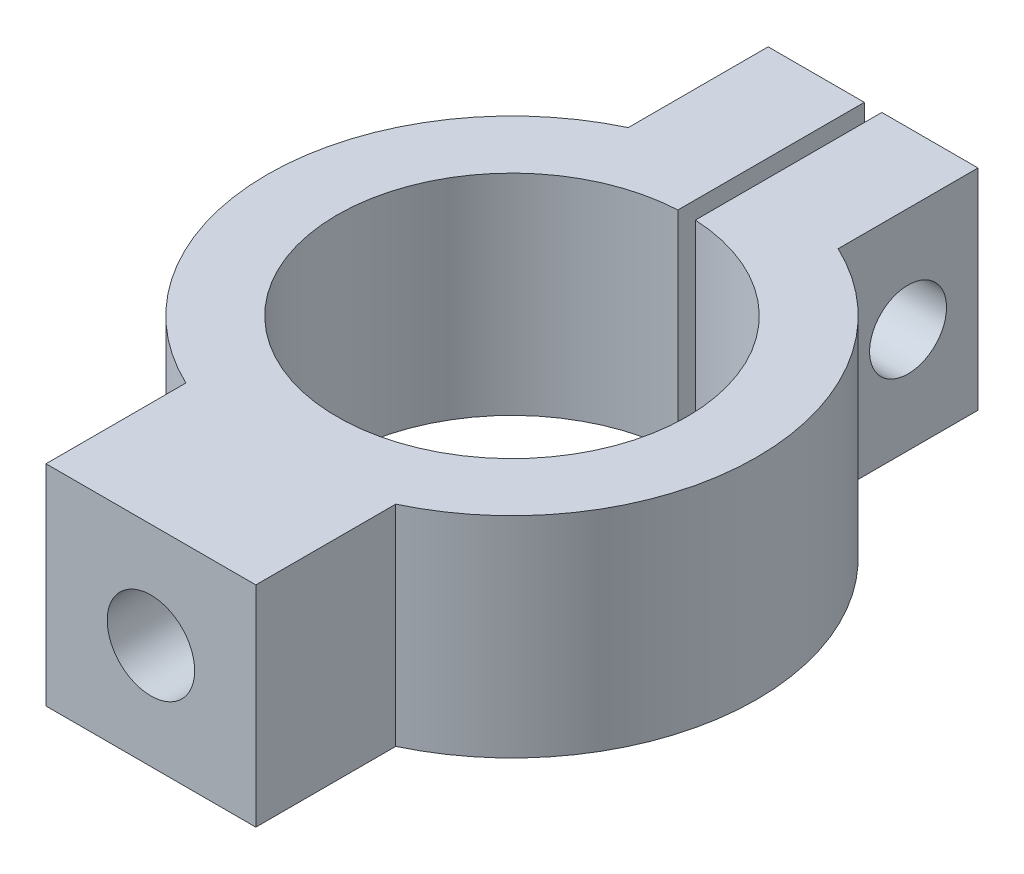
SolidWorks part; units mm, degrees
ref_plane "Front Plane" through (0, 0, 0) normal (0, 0, 1) x (1, 0, 0)
ref_plane "Top Plane" through (0, 0, 0) normal (0, 1, 0) x (1, 0, 0)
ref_plane "Right Plane" through (0, 0, 0) normal (1, 0, 0) x (0, 0, -1)
sketch "Loop Sketch" plane through (0, 0, 0) normal (0, 1, 0) x (1, 0, 0)
  circle A0 centre (0, 0) radius 7
  circle A1 centre (0, 0) radius 5
  dimension "D1" = 14
  dimension "D2" = 10
extrude "Loop Extrude" add sketch "Loop Sketch" along normal blind 6
sketch "Block Sketch" plane through (0, 0, 0) normal (0, 1, 0) x (1, 0, 0)
  line L1 (-3, -10.3246) -> (3, -10.3246)
  line L2 (-3, -10.3246) -> (-3, -6.3246)
  line L3 (-3, -6.3246) -> (3, -6.3246)
  line L4 (3, -10.3246) -> (3, -6.3246)
  line L5 (-3, -10.3246) -> (3, -6.3246) construction
  line L6 (-3, -6.3246) -> (3, -10.3246) construction
  line L7 (3, 10.3246) -> (-3, 10.3246)
  line L8 (3, 10.3246) -> (3, 6.3246)
  line L9 (3, 6.3246) -> (-3, 6.3246)
  line L10 (-3, 10.3246) -> (-3, 6.3246)
  line L11 (3, 10.3246) -> (-3, 6.3246) construction
  line L12 (3, 6.3246) -> (-3, 10.3246) construction
  circle A0 centre (0, 0) radius 7 construction
  circle A2 centre (0, 0) radius 7 construction
  point P0 (0, -8.3246)
  point P7 (0, 8.3246)
  dimension "D1" = 6
  dimension "D2" = 4
extrude "Block Extrude" add sketch "Block Sketch" along normal up to surface (6 mm away) up to face at (0, 6, 7)
sketch "Slot Sketch" plane through (0, 0, 0) normal (0, 1, 0) x (1, 0, 0)
  line L5 (3, 10.3246) -> (-3, 10.3246) construction
  line L6 (-0.25, 4.9937) -> (0.25, 4.9937)
  line L7 (-0.25, 4.9937) -> (-0.25, 10.3246)
  line L8 (-0.25, 10.3246) -> (0.25, 10.3246)
  line L9 (0.25, 4.9937) -> (0.25, 10.3246)
  line L10 (-0.25, 4.9937) -> (0.25, 10.3246) construction
  line L11 (-0.25, 10.3246) -> (0.25, 4.9937) construction
  circle A0 centre (0, 0) radius 5 construction
  point P0 (0, 7.6592)
  dimension "D1" = 0.5
extrude "Slot Cut" cut sketch "Slot Sketch" along normal up to surface (6 mm away) up to face at (0, 6, 0)
sketch "M3 Hole Location" plane through (0, 0, 0) normal (0, 0, 1) x (1, 0, 0)
  line L0 (-3, 6) -> (-3, 0) construction
  point P0 (0, 3)
  point P4 (-3, 3)
hole_wizard "M3x0.5 Tapped Hole1" positions "Sketch5" profile "Sketch6" tap size "M3x0.5" standard "ANSI Metric"
sketch "Sketch5" plane through (0, 0, 10.3246) normal (0, 0, 1) x (1, 0, 0)
  point P0 (0, 3)
sketch "Sketch6" plane through (0, 3, 10.3246) normal (1, 0, 0) x (0, -1, 0)
  line L0 (0, 0) -> (0, 4.7511)
  line L1 (0, 4.7511) -> (1.25, 4)
  line L2 (1.25, 4) -> (1.25, 0)
  line L5 (1.25, 0) -> (0, 0)
  line L10 (0, 4.7511) -> (-1.25, 4) construction
  line L11 (0, -6.35) -> (0, 107.95) construction
  dimension "Tap Drill Dia." = 2.5
  dimension "Tap Drill Depth" = 4
  dimension "Drill Angle" = 118
cosmetic thread "Hole Thread1" parameters "D1"=6, "D2"=3
sketch "M2 Hole Location" plane through (0, 0, 0) normal (1, 0, 0) x (0, 0, -1)
  line L1 (10.3246, 6) -> (10.3246, 0) construction
  line L2 (6.3246, 0) -> (10.3246, 0) construction
  point P0 (8.3246, 3)
  dimension "D1" = 2
  dimension "D2" = 3
hole_wizard "Ø2.2 (2.2) Diameter Hole1" positions "Sketch8" profile "Sketch9" hole size "Ø2.2" standard "ANSI Metric"
sketch "Sketch8" plane through (3, 0, 0) normal (1, 0, 0) x (0, 0, -1)
  point P0 (8.3246, 3)
sketch "Sketch9" plane through (3, 3, -8.3246) normal (0, 1, 0) x (0, 0, -1)
  line L0 (0, 0) -> (0, 3.4099)
  line L1 (0, 3.4099) -> (1.1, 2.749)
  line L2 (1.1, 2.749) -> (1.1, 0)
  line L5 (1.1, 0) -> (0, 0)
  line L10 (0, 3.4099) -> (-1.1, 2.749) construction
  line L11 (0, -6.35) -> (0, 107.95) construction
  dimension "Hole Dia." = 2.2
  dimension "Hole Depth" = 2.749
  dimension "Drill Angle" = 118
hole_wizard "M2x0.4 Tapped Hole1" positions "Sketch10" profile "Sketch12" tap size "M2x0.4" standard "ANSI Metric"
sketch "Sketch10" plane through (-0.25, 0, 0) normal (1, 0, 0) x (0, 0, -1)
  point P0 (8.3246, 3)
sketch "Sketch12" plane through (-0.25, 3, -8.3246) normal (0, 1, 0) x (0, 0, -1)
  line L0 (0, 0) -> (0, 3.2297)
  line L1 (0, 3.2297) -> (0.8, 2.749)
  line L2 (0.8, 2.749) -> (0.8, 0)
  line L5 (0.8, 0) -> (0, 0)
  line L10 (0, 3.2297) -> (-0.8, 2.749) construction
  line L11 (0, -6.35) -> (0, 107.95) construction
  dimension "Tap Drill Dia." = 1.6
  dimension "Tap Drill Depth" = 2.749
  dimension "Drill Angle" = 118
cosmetic thread "Hole Thread2" parameters "D1"=4, "D2"=2
